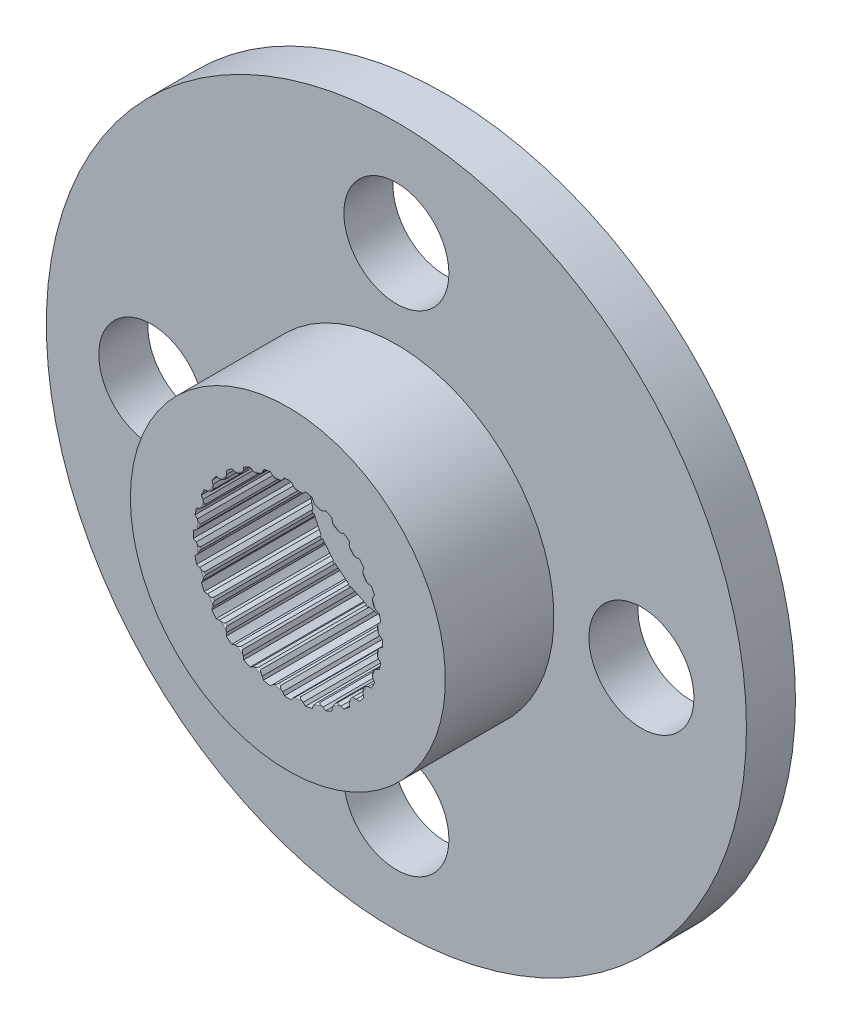
SolidWorks part; units mm, degrees
material "Beryllium"
ref_plane "Alzado" through (0, 0, 0) normal (0, 0, 1) x (1, 0, 0)
ref_plane "Planta" through (0, 0, 0) normal (0, 1, 0) x (1, 0, 0)
ref_plane "Vista lateral" through (0, 0, 0) normal (1, 0, 0) x (0, 0, -1)
sketch "Croquis1" plane through (0, 0, 0) normal (0, 0, 1) x (1, 0, 0)
  circle A0 centre (0, 0) radius 7 construction
  circle A1 centre (0, 0) radius 10
  circle A2 centre (-7, 0) radius 1.5
  circle A3 centre (0, 7) radius 1.5
  circle A4 centre (0, -7) radius 1.5
  circle A5 centre (7, 0) radius 1.5
  circle A6 centre (0, 0) radius 1.5
  dimension "D1" = 14
  dimension "D2" = 20
  dimension "D3" = 3
extrude "Saliente-Extruir1" add sketch "Croquis1" along normal blind 1.4
sketch "Croquis3" plane through (0, 0, 1.4) normal (0, 0, 1) x (1, 0, 0)
  line L0 (0, 0) -> (0, 4.1004) construction
  circle A0 centre (0, 0) radius 4.5
  circle A1 centre (0, 0) radius 2.55
  dimension "D1" = 9
  dimension "D2" = 5.1
extrude "Saliente-Extruir3" add sketch "Croquis3" along normal blind 3.1
sketch "Croquis4" plane through (0, 0, 4.5) normal (0, 0, 1) x (1, 0, 0)
  line L0 (0, 0) -> (0, 3.2695) construction
  line L1 (0.246, 2.4975) -> (-0.246, 2.4975)
  line L2 (-0.246, 2.4975) -> (-0.25, 2.5377)
  line L3 (-0.25, 2.5377) -> (-0.15, 2.62)
  line L4 (-0.15, 2.62) -> (-0.1, 2.6981)
  line L5 (0.246, 2.4975) -> (0.25, 2.5377)
  line L6 (0.25, 2.5377) -> (0.15, 2.62)
  line L7 (0.15, 2.62) -> (0.1, 2.6981)
  circle A0 centre (0, 0) radius 2.55
  circle A1 centre (0, 0) radius 2.7
  point P13 (0, 2.4975)
  point P15 (0, 2.4975)
  circle M7 centre (0, 0) radius 2.55
  dimension "D1" = 5.1
  dimension "D2" = 5.4
  dimension "D7" = 2.4975
  dimension "D3" = 0.25
  dimension "D4" = 0.15
  dimension "D5" = 0.1
  dimension "D6" = 2.62
extrude "Cortar-Extruir2" cut sketch "Croquis4" against normal blind 3.4 contours L0 A0 L6 L7 A1 | L0 A1 L4 L3 M7 | L0 L1 L5 A0 | L1 L0 L2 M7
fillet "Redondeo1" radius 0.05 1 edges at (0, -2.55, 4.5)
pattern_circular "MatrizC1" count 28 over 360 about axis through (0, 0, 0) along (0, 0, 1) of "Cortar-Extruir2"
